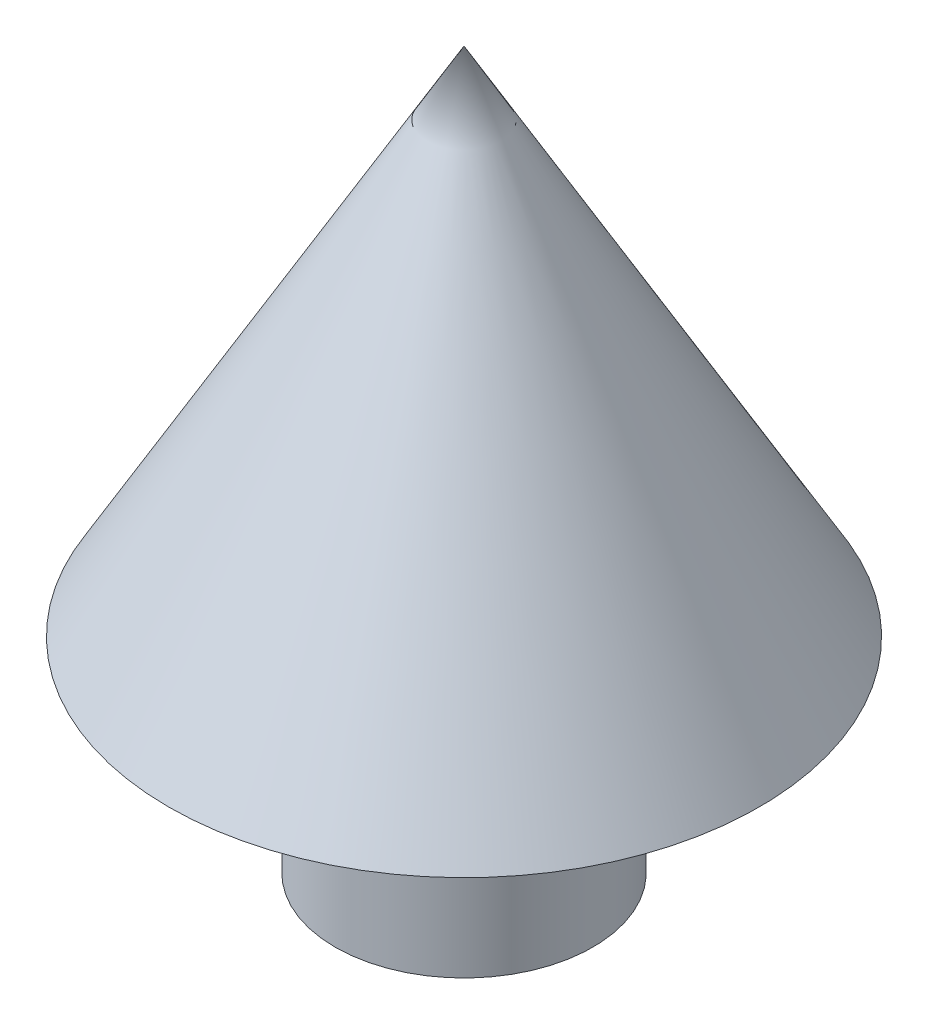
SolidWorks part; units mm, degrees
ref_plane "Front Plane" through (0, 0, 0) normal (0, 0, 1) x (1, 0, 0)
ref_plane "Top Plane" through (0, 0, 0) normal (0, 1, 0) x (1, 0, 0)
ref_plane "Right Plane" through (0, 0, 0) normal (1, 0, 0) x (0, 0, -1)
sketch "Sketch2" plane through (0, 0, 0) normal (1, 0, 0) x (0, 0, -1)
  line L0 (0, 0) -> (0, 35)
  line L1 (0, 35) -> (-14.4338, 10)
  line L2 (-14.4338, 10) -> (-6.3, 10)
  line L3 (-6.3, 10) -> (-6.3, 0)
  line L4 (-6.3, 0) -> (0, 0)
  line L5 (0, 0) -> (0, 62.9834) construction
  dimension "D1" = 6.3
  dimension "D2" = 30
  dimension "D3" = 35
  dimension "D4" = 10
revolve "Revolve1" add sketch "Sketch2" angle 360 about L5
